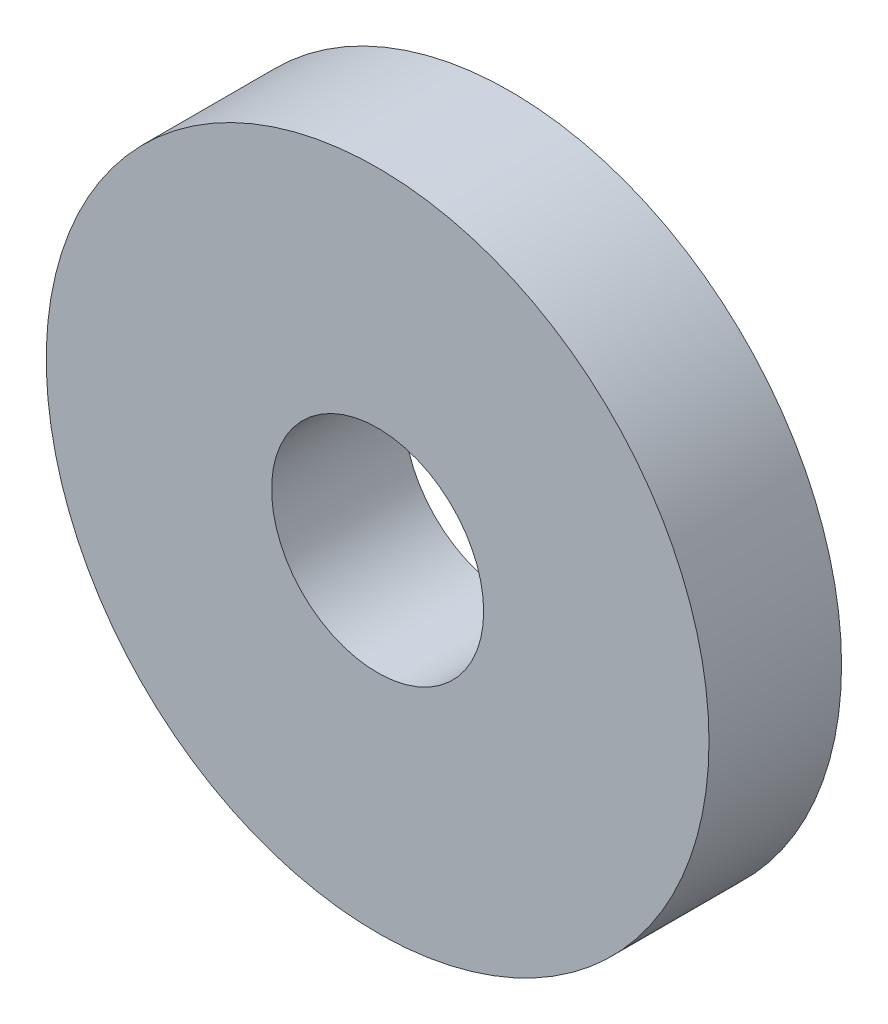
SolidWorks part; units mm, degrees
ref_plane "Front Plane" through (0, 0, 0) normal (0, 0, 1) x (1, 0, 0)
ref_plane "Top Plane" through (0, 0, 0) normal (0, 1, 0) x (1, 0, 0)
ref_plane "Right Plane" through (0, 0, 0) normal (1, 0, 0) x (0, 0, -1)
sketch "Sketch1" plane through (0, 0, 0) normal (0, 0, 1) x (1, 0, 0)
  circle A0 centre (0, 0) radius 12.5
  circle A1 centre (0, 0) radius 4
  dimension "D1" = 25
  dimension "D2" = 8
extrude "Boss-Extrude1" add sketch "Sketch1" along normal blind 5
